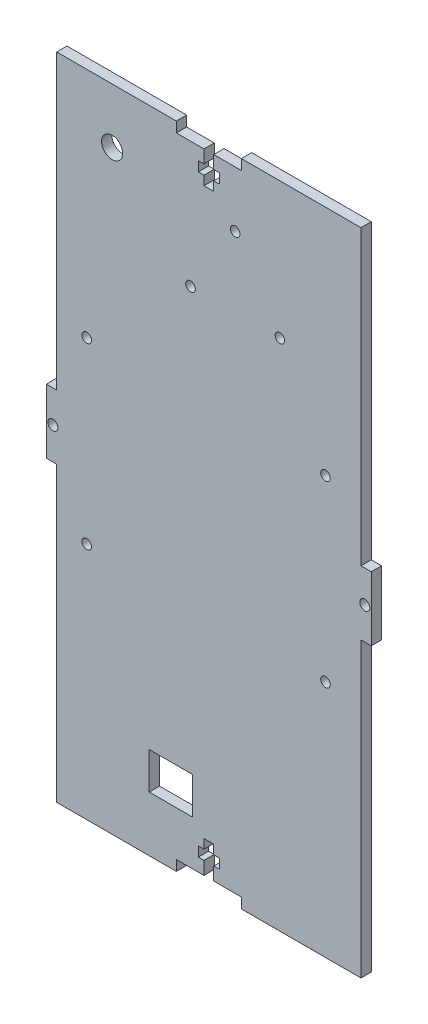
SolidWorks part; units mm, degrees
ref_plane "Front Plane" through (0, 0, 0) normal (0, 0, 1) x (1, 0, 0)
ref_plane "Top Plane" through (0, 0, 0) normal (0, 1, 0) x (1, 0, 0)
ref_plane "Right Plane" through (0, 0, 0) normal (1, 0, 0) x (0, 0, -1)
sketch "Sketch1" plane through (0, 0, 0) normal (0, 0, 1) x (1, 0, 0)
  line L0 (0, 40) -> (0, -40) construction
  line L5 (-50, -100) -> (50, 100) construction
  line L6 (-50, 100) -> (50, -100) construction
  line L7 (-100, 0) -> (100, 0) construction
  line L32 (-50, 100) -> (50, 100)
  line L35 (50, 100) -> (50, -100)
  line L36 (50, -100) -> (-50, -100)
  line L37 (-50, -100) -> (-50, 100)
  point P0 (0, 0)
  dimension "D1" = 100
  dimension "D2" = 200
extrude "Boss-Extrude2" add sketch "Sketch1" along normal blind 3.18
sketch "Sketch2" plane through (0, 0, 3.18) normal (0, 0, 1) x (1, 0, 0)
  line L0 (0, -100) -> (0, 100) construction
  line L1 (-123.0225, 0) -> (147.0753, 0) construction
  line L2 (50, 100) -> (-50, 100) construction
  line L4 (-10, 100) -> (-10, 96.82)
  line L5 (-10, 96.82) -> (-1.5, 96.82)
  line L6 (10, 100) -> (10, 96.82)
  line L7 (1.5, 96.82) -> (10, 96.82)
  line L9 (-1.5, 96.82) -> (-1.5, 92.82)
  line L10 (-1.5, 87) -> (1.5, 87)
  line L11 (1.5, 96.82) -> (1.5, 92.82)
  line L12 (-3.25, 92.82) -> (-1.5, 92.82)
  line L13 (-3.25, 92.82) -> (-3.25, 89.82)
  line L14 (-3.25, 89.82) -> (-1.5, 89.82)
  line L15 (3.25, 92.82) -> (3.25, 89.82)
  line L16 (1.5, 92.82) -> (3.25, 92.82)
  line L17 (-1.5, 89.82) -> (-1.5, 87)
  line L18 (1.5, 89.82) -> (1.5, 87)
  line L19 (1.5, 89.82) -> (3.25, 89.82)
  line L20 (-10, 100) -> (10, 100)
  line L21 (-50, -100) -> (50, -100) construction
  line L22 (-50, 100) -> (-50, -100) construction
  line L23 (-50, 9.875) -> (-46.82, 9.875)
  line L24 (-50, 9.875) -> (-50, 100)
  line L25 (-50, 100) -> (-46.82, 100)
  line L26 (-46.82, 9.875) -> (-46.82, 100)
  line L28 (-50, -9.875) -> (-46.82, -9.875)
  line L29 (-50, -9.875) -> (-50, -100)
  line L30 (-50, -100) -> (-46.82, -100)
  line L31 (-46.82, -9.875) -> (-46.82, -100)
  circle A0 centre (-48, 0) radius 1.55
  dimension "D11" = 3.1
  dimension "D12" = 2
  dimension "D1" = 4
  dimension "D2" = 3
  dimension "D3" = 3
  dimension "D4" = 20
  dimension "D5" = 6.5
  dimension "D6" = 3.18
  dimension "D7" = 13
  dimension "D8" = 19.75
  dimension "D9" = 3.18
  dimension "D10" = 3.18
extrude "Cut-Extrude1" cut sketch "Sketch2" against normal through all
mirror "Mirror1" about plane through (0, 0, 0) normal (0, 1, 0) of "Cut-Extrude1"
mirror "Mirror3" about plane through (0, 0, 0) normal (1, 0, 0) of "Cut-Extrude1"
sketch "Sketch4" plane through (0, 0, 3.18) normal (0, 0, 1) x (1, 0, 0)
  line L5 (-18.3522, -83.0261) -> (-5.0022, -83.0261)
  line L6 (-18.3522, -83.0261) -> (-18.3522, -71.6761)
  line L7 (-18.3522, -71.6761) -> (-5.0022, -71.6761)
  line L8 (-5.0022, -83.0261) -> (-5.0022, -71.6761)
  dimension "D1" = 13.35
  dimension "D2" = 11.35
sketch "Sketch5" plane through (0, 0, 3.18) normal (0, 0, 1) x (1, 0, 0)
  circle A0 centre (-37.5809, 28.4641) radius 1.47
  circle A1 centre (35.9045, 28.4641) radius 1.47
  circle A2 centre (-37.5809, -26.5359) radius 1.47
  circle A3 centre (35.9045, -26.5359) radius 1.47
  circle A4 centre (-37.5809, 28.4641) radius 1.47 construction
  circle A5 centre (35.9045, 28.4641) radius 1.47 construction
  circle A6 centre (35.9045, -26.5359) radius 1.47 construction
  circle A8 centre (-37.5809, -26.5359) radius 1.47 construction
extrude "Cut-Extrude4" cut sketch "Sketch5" against normal through all
sketch "Sketch6" plane through (0, 0, 3.18) normal (0, 0, 1) x (1, 0, 0)
  circle A0 centre (-5.6383, 58.12) radius 1.47
  circle A1 centre (8.1117, 79.62) radius 1.47
  circle A2 centre (21.8617, 58.12) radius 1.47
  circle A3 centre (-5.6383, 58.12) radius 1.4 construction
  circle A4 centre (8.1117, 79.62) radius 1.4 construction
  circle A5 centre (21.8617, 58.12) radius 1.4 construction
  dimension "D1" = 2.94
extrude "Cut-Extrude5" cut sketch "Sketch6" against normal through all
extrude "Cut-Extrude7" cut sketch "Sketch4" against normal through all
sketch "Sketch7" plane through (0, 0, 3.18) normal (0, 0, 1) x (1, 0, 0)
  circle A0 centre (-29.7603, 83.0862) radius 3.25
  circle A1 centre (-29.7603, 83.0862) radius 2.4 construction
  dimension "D1" = 6.5
extrude "Cut-Extrude8" cut sketch "Sketch7" against normal through all
